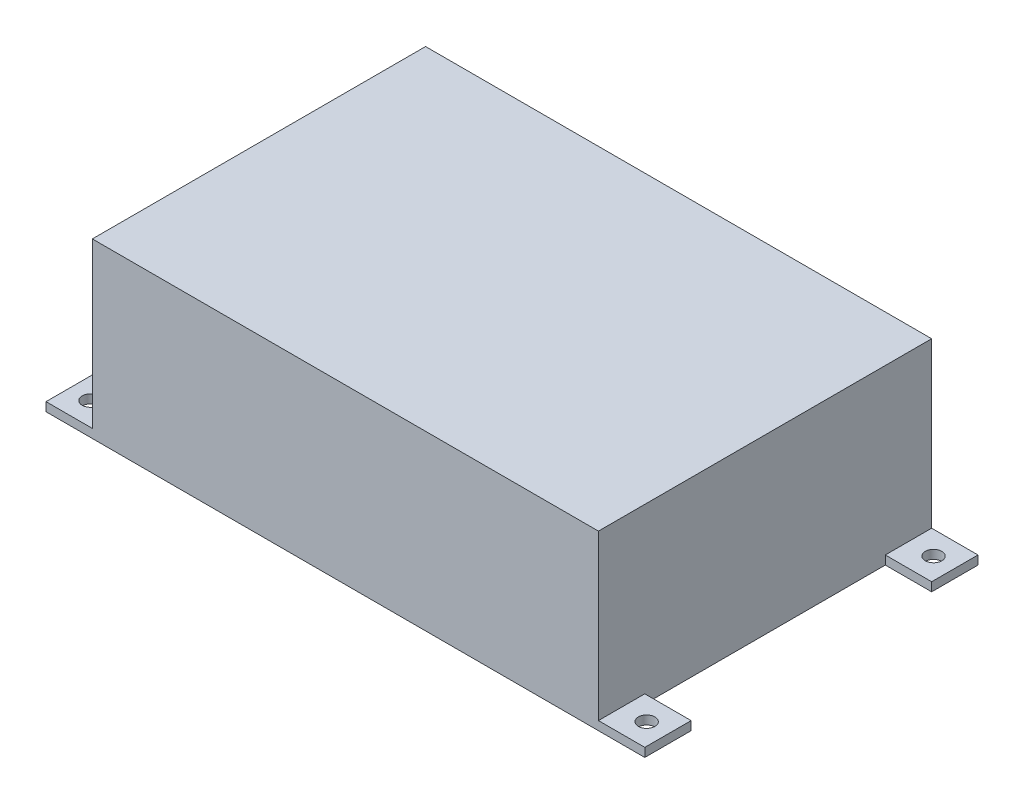
SolidWorks part; units mm, degrees
ref_plane "Front Plane" through (0, 0, 0) normal (0, 0, 1) x (1, 0, 0)
ref_plane "Top Plane" through (0, 0, 0) normal (0, 1, 0) x (1, 0, 0)
ref_plane "Right Plane" through (0, 0, 0) normal (1, 0, 0) x (0, 0, -1)
sketch "Sketch1" plane through (0, 0, 0) normal (0, 1, 0) x (1, 0, 0)
  line L1 (0, 0) -> (202, 0)
  line L2 (0, 0) -> (0, 133)
  line L3 (0, 133) -> (202, 133)
  line L4 (202, 0) -> (202, 133)
  dimension "D1" = 133
  dimension "D2" = 202
extrude "Boss-Extrude1" add sketch "Sketch1" along normal blind 69
sketch "Sketch2" plane through (0, 0, 0) normal (0, 1, 0) x (1, 0, 0)
  line L0 (202, 133) -> (0, 133) construction
  line L1 (0, 133) -> (-18.5, 133)
  line L2 (0, 133) -> (0, 114.5)
  line L3 (0, 114.5) -> (-18.5, 114.5)
  line L4 (-18.5, 133) -> (-18.5, 114.5)
  line L5 (0, 133) -> (0, 0) construction
  line L7 (0, 0) -> (-18.5, 0)
  line L8 (0, 0) -> (0, 18.5)
  line L9 (0, 18.5) -> (-18.5, 18.5)
  line L10 (-18.5, 0) -> (-18.5, 18.5)
  line L11 (202, 0) -> (220.5, 0)
  line L12 (202, 0) -> (202, 18.5)
  line L13 (202, 18.5) -> (220.5, 18.5)
  line L14 (220.5, 0) -> (220.5, 18.5)
  line L15 (202, 133) -> (220.5, 133)
  line L16 (202, 133) -> (202, 114.5)
  line L17 (202, 114.5) -> (220.5, 114.5)
  line L18 (220.5, 133) -> (220.5, 114.5)
  dimension "D1" = 239
  dimension "D2" = 18.5
extrude "Boss-Extrude2" add sketch "Sketch2" along normal blind 3.5
hole_wizard "M6 Clearance Hole1" positions "Sketch4" profile "Sketch3" hole size "M6" standard "ANSI Metric" end condition through all
sketch "Sketch4" plane through (0, 3.5, 0) normal (0, 1, 0) x (1, 0, 0)
  line L1 (-18.5, 133) -> (-18.5, 114.5) construction
  line L3 (-18.5, 18.5) -> (-18.5, 0) construction
  line L4 (202, 133) -> (0, 133) construction
  point P0 (-10, 123.75)
  point P2 (-10, 9.25)
  point P4 (212, 9.25)
  point P6 (212, 123.75)
  point P14 (-18.5, 123.75)
  point P25 (-18.5, 9.25)
  point P29 (101, 133)
  dimension "D1" = 222
  dimension "D2" = 111
sketch "Sketch3" plane through (-10, 3.5, -123.75) normal (1, 0, 0) x (0, 0, 1)
  line L0 (0, 0) -> (0, 3.5001)
  line L1 (0, 3.5001) -> (3.3, 3.5001)
  line L2 (3.3, 3.5001) -> (3.3, 0)
  line L5 (3.3, 0) -> (0, 0)
  line L11 (0, -6.35) -> (0, 107.95) construction
  dimension "Thru Hole Dia." = 6.6
  dimension "Thru Hole Depth" = 3.5001
equation "\"D2@Sketch4\"=\"D1@Sketch4\"/2"
